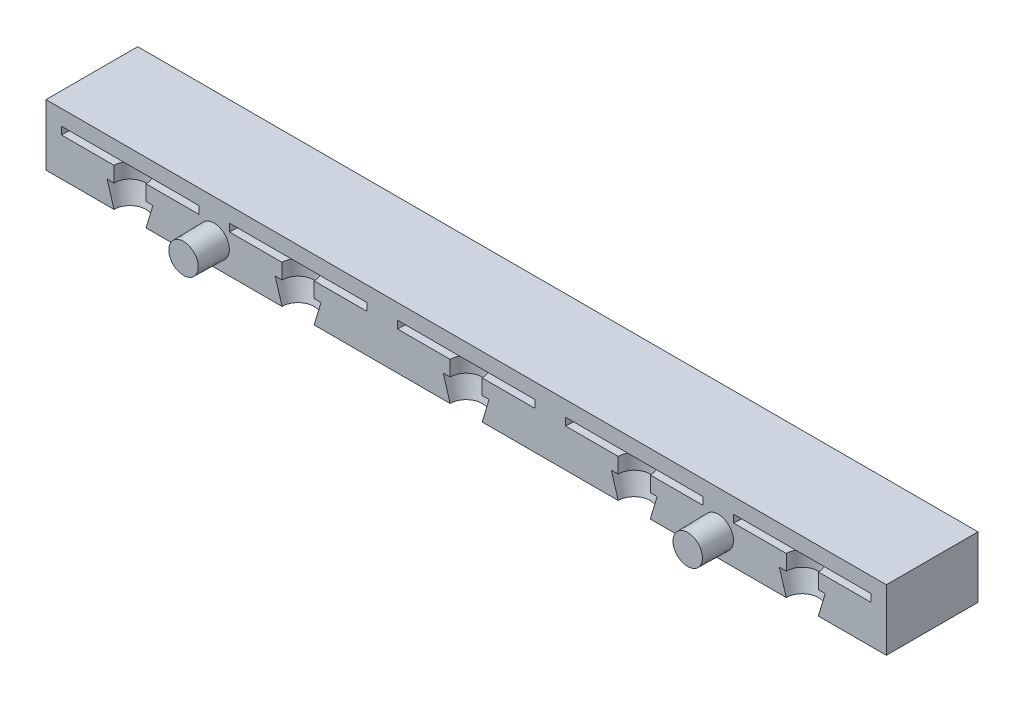
SolidWorks part; units mm, degrees
ref_plane "Front Plane" through (0, 0, 0) normal (0, 0, 1) x (1, 0, 0)
ref_plane "Top Plane" through (0, 0, 0) normal (0, 1, 0) x (1, 0, 0)
ref_plane "Right Plane" through (0, 0, 0) normal (1, 0, 0) x (0, 0, -1)
sketch "Sketch2" plane through (0, 0, 0) normal (0, 0, 1) x (1, 0, 0)
  line L1 (0, 0) -> (110, 0)
  line L2 (0, 0) -> (0, 8)
  line L3 (0, 8) -> (110, 8)
  line L4 (110, 0) -> (110, 8)
  dimension "D1" = 8
  dimension "D2" = 110
extrude "Boss-Extrude1" add sketch "Sketch2" against normal blind 12
sketch "Sketch3" plane through (0, 0, 0) normal (0, 0, 1) x (1, 0, 0)
  line L2 (8, 3) -> (8.9, 3)
  line L3 (8.9, 3) -> (8.9, 5)
  line L4 (8.9, 5) -> (2, 5)
  line L7 (11, 6) -> (11, 0) construction
  line L8 (8, 3) -> (8.9, 0)
  line L9 (8.9, 0) -> (11, 0)
  line L10 (0, 0) -> (110, 0) construction
  line L11 (11, 0) -> (11, 6)
  line L12 (2, 5) -> (2, 6)
  line L13 (2, 6) -> (11, 6)
  dimension "D1" = 2
  dimension "D2" = 0
  dimension "D3" = 2.1
  dimension "D4" = 3
  dimension "D5" = 1
  dimension "D6" = 3
  dimension "D7" = 2.1
  dimension "D8" = 0
revolve "Cut-Revolve1" cut sketch "Sketch3" angle 360 about L7
pattern_linear "LPattern1" count 5 spacing 22 along (1, 0, 0) of "Cut-Revolve1"
sketch "Sketch4" plane through (0, 0, 0) normal (0, 0, 1) x (1, 0, 0)
  line L0 (20, 8) -> (2, 8) construction
  line L1 (11, 0) -> (11, 8) construction
  line L2 (8.9, 0) -> (13.1, 0) construction
  line L3 (110, 0) -> (110, 8) construction
  line L4 (0, 0) -> (8.9, 0) construction
  line L7 (0, 0) -> (8.9, 0) construction
  circle A0 centre (22, 3) radius 2
  circle A2 centre (88, 3) radius 2
  point P11 (88, 3)
  dimension "D2" = 4
  dimension "D1" = 22
  dimension "D3" = 3
  dimension "D4" = 22
  dimension "D5" = 3
extrude "Boss-Extrude2" add sketch "Sketch4" along normal blind 4 draft 1
equation "\"D4@Sketch4\"=\"D1@Sketch4\""
equation "\"D5@Sketch4\"=\"D3@Sketch4\""
